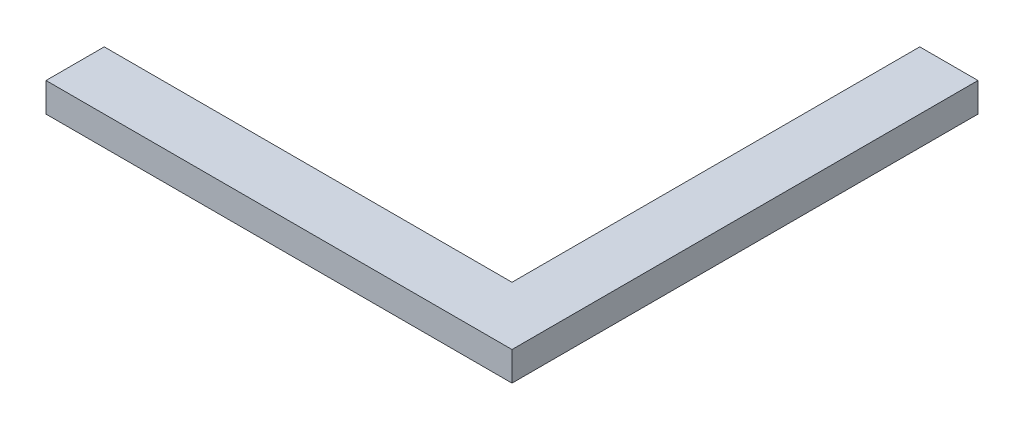
SolidWorks part; units mm, degrees
ref_plane "Front Plane" through (0, 0, 0) normal (0, 0, 1) x (1, 0, 0)
ref_plane "Top Plane" through (0, 0, 0) normal (0, 1, 0) x (1, 0, 0)
ref_plane "Right Plane" through (0, 0, 0) normal (1, 0, 0) x (0, 0, -1)
sketch "Sketch1" plane through (0, 0, 0) normal (0, 1, 0) x (1, 0, 0)
  line L0 (-80, 80) -> (80, -80) construction
  line L1 (-80, 80) -> (80, 80) construction
  line L2 (-80, 80) -> (-80, -80) construction
  line L3 (-80, -80) -> (80, -80) construction
  line L4 (80, 80) -> (80, -80) construction
  line L5 (-80, -80) -> (80, -80)
  line L6 (80, -80) -> (80, 80)
  line L7 (80, 80) -> (60, 80)
  line L8 (60, 80) -> (60, -60)
  line L9 (60, -60) -> (-80, -60)
  line L10 (-80, -60) -> (-80, -80)
  dimension "D1" = 160
  dimension "D2" = 160
  dimension "D3" = 20
  dimension "D4" = 20
extrude "Boss-Extrude1" add sketch "Sketch1" along normal blind 10
